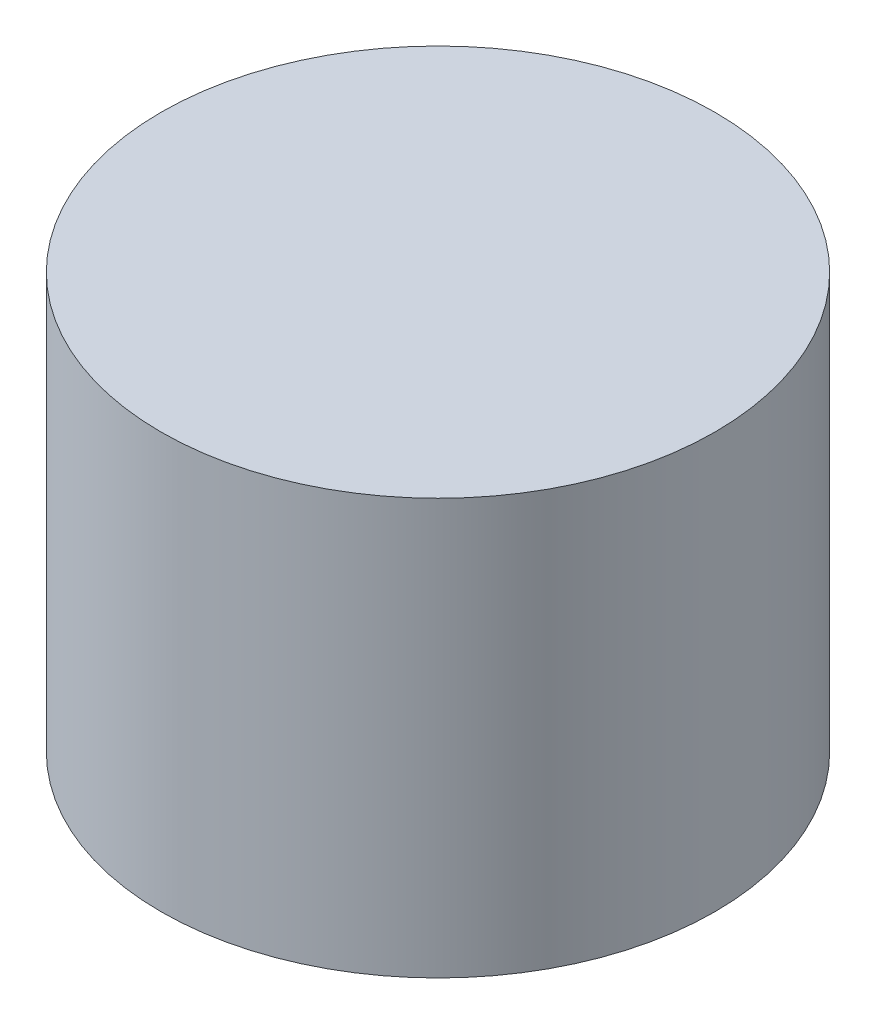
SolidWorks part; units mm, degrees
material "5052-O"
ref_plane "正面" through (0, 0, 0) normal (0, 0, 1) x (1, 0, 0)
ref_plane "平面" through (0, 0, 0) normal (0, 1, 0) x (1, 0, 0)
ref_plane "右側面" through (0, 0, 0) normal (1, 0, 0) x (0, 0, -1)
sketch "ｽｹｯﾁ1" plane through (0, 0, 0) normal (0, 1, 0) x (1, 0, 0)
  circle A0 centre (0, 0) radius 3.5
extrude "ﾎﾞｽ - 押し出し1" add sketch "ｽｹｯﾁ1" along normal blind 5.25
